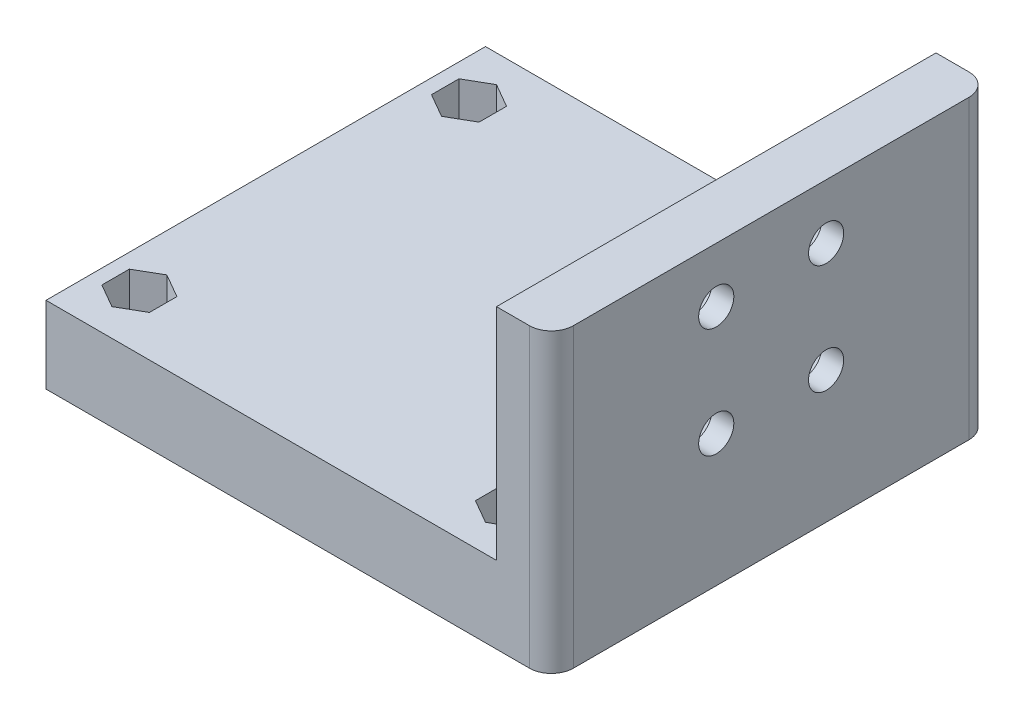
SolidWorks part; units mm, degrees
ref_plane "Plan de face" through (0, 0, 0) normal (0, 0, 1) x (1, 0, 0)
ref_plane "Plan de dessus" through (0, 0, 0) normal (0, 1, 0) x (1, 0, 0)
ref_plane "Plan de droite" through (0, 0, 0) normal (1, 0, 0) x (0, 0, -1)
sketch "Esquisse1" plane through (0, 0, 0) normal (0, 1, 0) x (1, 0, 0)
  line L1 (0, 20) -> (-5, 20)
  line L2 (0, 20) -> (0, -20)
  line L3 (0, -20) -> (-5, -20)
  line L4 (-5, 20) -> (-5, -20)
  dimension "D1" = 5
  dimension "D2" = 40
  dimension "D3" = 20
extrude "Boss.-Extru.1" add sketch "Esquisse1" against normal blind 27
sketch "Esquisse2" plane through (-5, 0, 0) normal (-1, 0, 0) x (0, 0, 1)
  line L0 (-20, -27) -> (-20, 0) construction
  line L1 (20, -27) -> (-20, -27)
  line L2 (20, -27) -> (20, -20)
  line L3 (20, -20) -> (-20, -20)
  line L4 (-20, -27) -> (-20, -20)
  dimension "D1" = 7
extrude "Boss.-Extru.2" add sketch "Esquisse2" along normal blind 41
fillet "Congé1" radius 2 2 edges at (0, -13.5, -20) (0, -13.5, 20)
sketch "Esquisse4" plane through (0, 0, 0) normal (1, 0, 0) x (0, 0, -1)
  circle A0 centre (-5, -5) radius 1.6
  circle A1 centre (5, -5) radius 1.6
  circle A2 centre (-5, -15) radius 1.6
  circle A3 centre (5, -15) radius 1.6
  dimension "D1" = 10
  dimension "D3" = 3.2
  dimension "D2" = 10
  dimension "D4" = 5
  dimension "D5" = 5
extrude "Enlèv. mat.-Extru.1" cut sketch "Esquisse4" against normal up to next
sketch "Esquisse7" plane through (-5, 0, 0) normal (-1, 0, 0) x (0, 0, 1)
  line L1 (-3.25, -8.0311) -> (-1.5, -5)
  line L2 (-1.5, -5) -> (-3.25, -1.9689)
  line L3 (-3.25, -1.9689) -> (-6.75, -1.9689)
  line L4 (-6.75, -1.9689) -> (-8.5, -5)
  line L5 (-8.5, -5) -> (-6.75, -8.0311)
  line L6 (-6.75, -8.0311) -> (-3.25, -8.0311)
  line L7 (3.25, -1.9689) -> (1.5, -5)
  line L8 (1.5, -5) -> (3.25, -8.0311)
  line L9 (3.25, -8.0311) -> (6.75, -8.0311)
  line L10 (6.75, -8.0311) -> (8.5, -5)
  line L11 (8.5, -5) -> (6.75, -1.9689)
  line L12 (6.75, -1.9689) -> (3.25, -1.9689)
  line L13 (-3.25, -18.0311) -> (-1.5, -15)
  line L14 (-1.5, -15) -> (-3.25, -11.9689)
  line L15 (-3.25, -11.9689) -> (-6.75, -11.9689)
  line L16 (-6.75, -11.9689) -> (-8.5, -15)
  line L17 (-8.5, -15) -> (-6.75, -18.0311)
  line L18 (-6.75, -18.0311) -> (-3.25, -18.0311)
  line L19 (8.5, -15) -> (6.75, -11.9689)
  line L20 (6.75, -11.9689) -> (3.25, -11.9689)
  line L21 (3.25, -11.9689) -> (1.5, -15)
  line L22 (1.5, -15) -> (3.25, -18.0311)
  line L23 (3.25, -18.0311) -> (6.75, -18.0311)
  line L24 (6.75, -18.0311) -> (8.5, -15)
  line L25 (18, 0) -> (-18, 0) construction
  line L26 (-20, 0) -> (20, 0) construction
  circle A0 centre (-5, -5) radius 3.0311 construction
  circle A1 centre (5, -5) radius 3.0311 construction
  circle A2 centre (-5, -15) radius 3.0311 construction
  circle A3 centre (5, -15) radius 3.0311 construction
  circle A4 centre (5, -15) radius 1.6 construction
  dimension "D1" = 3.5
  dimension "D2" = 3.5
  dimension "D3" = 3.5
  dimension "D4" = 3.5
extrude "Enlèv. mat.-Extru.3" cut sketch "Esquisse7" against normal blind 3
sketch "Esquisse9" plane through (0, -20, 0) normal (0, 1, 0) x (1, 0, 0)
  line L0 (-5, -20) -> (-5, 20) construction
  line L1 (-46, -20) -> (-46, 20) construction
  line L4 (-46, -20) -> (-46, 20) construction
  circle A0 centre (-8.5, 15) radius 1.1
  circle A1 centre (-8.5, -15) radius 1.1
  circle A2 centre (-42.5, -15) radius 1.1
  circle A3 centre (-42.5, 15) radius 1.1
  point P8 (-46, 0)
  dimension "D1" = 2.2
  dimension "D5" = 15
  dimension "D2" = 3.5
  dimension "D3" = 3.5
  dimension "D4" = 30
extrude "Enlèv. mat.-Extru.5" cut sketch "Esquisse9" against normal through all
sketch "Esquisse8" plane through (0, -20, 0) normal (0, 1, 0) x (1, 0, 0)
  line L0 (-5, -20) -> (-5, 20) construction
  line L1 (-10.6651, 13.75) -> (-8.5, 12.5)
  line L2 (-8.5, 12.5) -> (-6.3349, 13.75)
  line L3 (-6.3349, 13.75) -> (-6.3349, 16.25)
  line L4 (-6.3349, 16.25) -> (-8.5, 17.5)
  line L5 (-8.5, 17.5) -> (-10.6651, 16.25)
  line L6 (-10.6651, 16.25) -> (-10.6651, 13.75)
  line L7 (-10.6651, -16.25) -> (-8.5, -17.5)
  line L8 (-8.5, -17.5) -> (-6.3349, -16.25)
  line L9 (-6.3349, -16.25) -> (-6.3349, -13.75)
  line L10 (-6.3349, -13.75) -> (-8.5, -12.5)
  line L11 (-8.5, -12.5) -> (-10.6651, -13.75)
  line L12 (-10.6651, -13.75) -> (-10.6651, -16.25)
  line L13 (-44.6651, -16.25) -> (-42.5, -17.5)
  line L14 (-42.5, -17.5) -> (-40.3349, -16.25)
  line L15 (-40.3349, -16.25) -> (-40.3349, -13.75)
  line L16 (-40.3349, -13.75) -> (-42.5, -12.5)
  line L17 (-42.5, -12.5) -> (-44.6651, -13.75)
  line L18 (-44.6651, -13.75) -> (-44.6651, -16.25)
  line L19 (-42.5, 12.5) -> (-40.3349, 13.75)
  line L20 (-40.3349, 13.75) -> (-40.3349, 16.25)
  line L21 (-40.3349, 16.25) -> (-42.5, 17.5)
  line L22 (-42.5, 17.5) -> (-44.6651, 16.25)
  line L23 (-44.6651, 16.25) -> (-44.6651, 13.75)
  line L24 (-44.6651, 13.75) -> (-42.5, 12.5)
  circle A0 centre (-8.5, 15) radius 2.1651 construction
  circle A1 centre (-8.5, -15) radius 2.1651 construction
  circle A2 centre (-42.5, -15) radius 2.1651 construction
  circle A3 centre (-42.5, 15) radius 2.1651 construction
  circle A4 centre (-8.5, 15) radius 1.1 construction
  circle A5 centre (-8.5, -15) radius 1.1 construction
  circle A7 centre (-42.5, 15) radius 1.1 construction
  dimension "D1" = 2.5
  dimension "D2" = 2.5
  dimension "D3" = 2.5
  dimension "D4" = 2.5
extrude "Enlèv. mat.-Extru.4" cut sketch "Esquisse8" against normal blind 4
